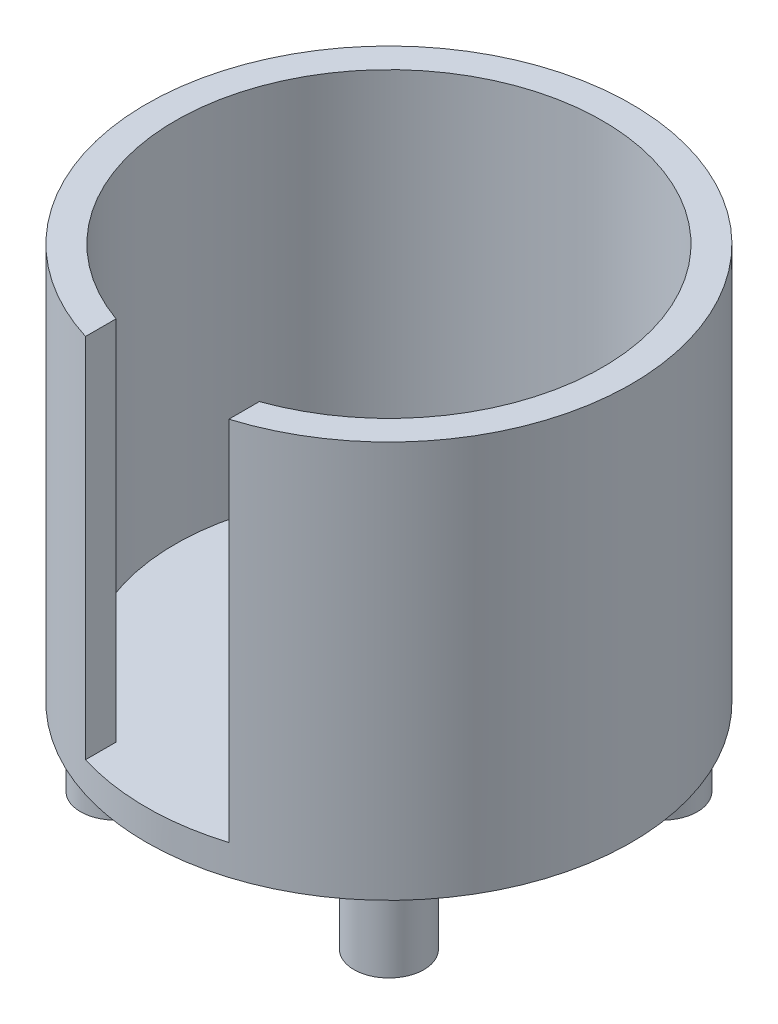
SolidWorks part; units mm, degrees
ref_plane "Front Plane" through (0, 0, 0) normal (0, 0, 1) x (1, 0, 0)
ref_plane "Top Plane" through (0, 0, 0) normal (0, 1, 0) x (1, 0, 0)
ref_plane "Right Plane" through (0, 0, 0) normal (1, 0, 0) x (0, 0, -1)
sketch "Sketch1" plane through (0, 0, 0) normal (0, 1, 0) x (1, 0, 0)
  circle A0 centre (0, 0) radius 22
  dimension "D1" = 44
extrude "Boss-Extrude1" add sketch "Sketch1" along normal blind 36
sketch "Sketch3" plane through (0, 36, 0) normal (0, 1, 0) x (1, 0, 0)
  circle A0 centre (0, 0) radius 19.375
  dimension "D1" = 38.75
extrude "Cut-Extrude1" cut sketch "Sketch3" against normal blind 33.25
sketch "Sketch4" plane through (0, 36, 0) normal (0, 1, 0) x (1, 0, 0)
  line L1 (6.5, -24.9538) -> (-6.5, -24.9538)
  line L2 (6.5, -24.9538) -> (6.5, -16.7122)
  line L3 (6.5, -16.7122) -> (-6.5, -16.7122)
  line L4 (-6.5, -24.9538) -> (-6.5, -16.7122)
  line L5 (6.5, -24.9538) -> (-6.5, -16.7122) construction
  line L6 (6.5, -16.7122) -> (-6.5, -24.9538) construction
  point P0 (0, -20.833)
  dimension "D1" = 13
extrude "Cut-Extrude2" cut sketch "Sketch4" against normal blind 33.25
sketch "Sketch5" plane through (0, 0, 0) normal (0, -1, 0) x (-1, 0, 0)
  circle A0 centre (12.3865, -12.4117) radius 3.175
  circle A2 centre (-12.4135, -12.4117) radius 3.175
  circle A3 centre (-12.4135, 12.3883) radius 3.175
  circle A4 centre (12.3865, 12.3883) radius 3.175
  circle A5 centre (0, 0) radius 22 construction
  dimension "D3" = 6.35
  dimension "D4" = 17.535
  dimension "D1" = 2
  dimension "D2" = 2
extrude "Boss-Extrude2" add sketch "Sketch5" along normal blind 7
